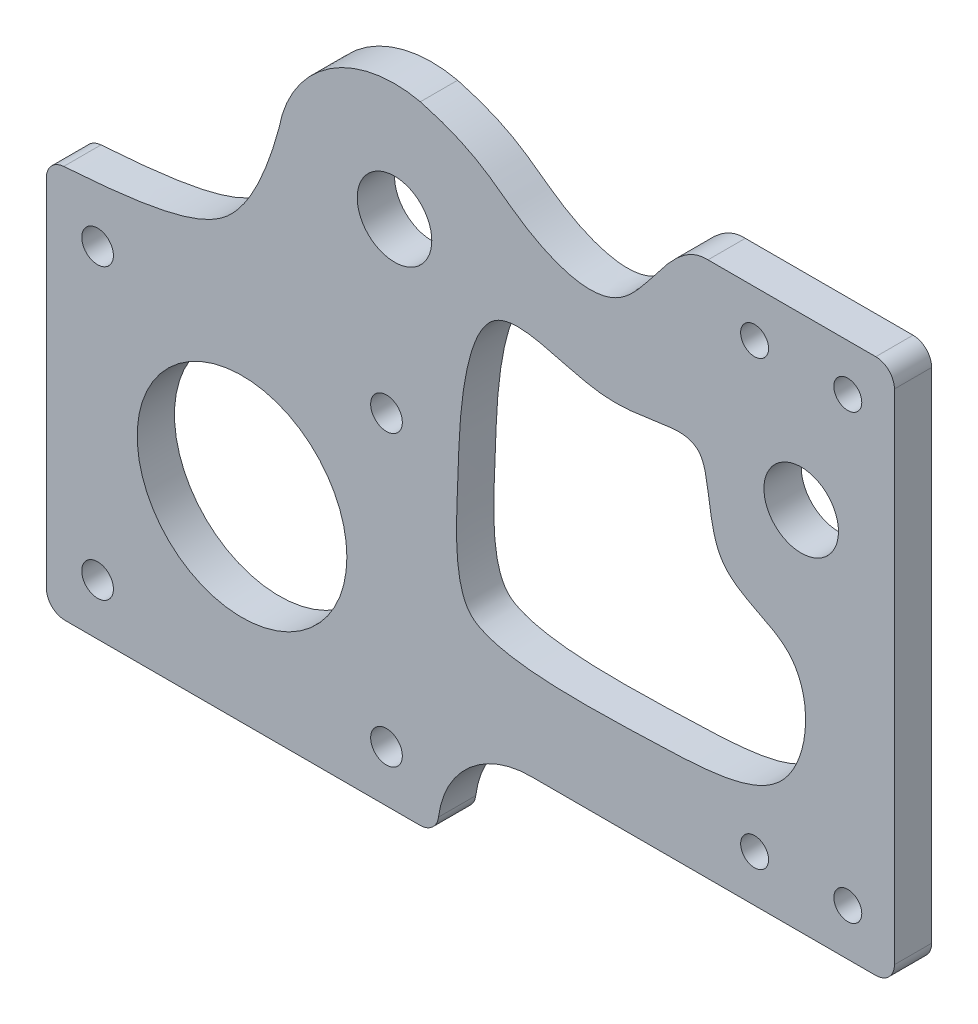
SolidWorks part; units mm, degrees
ref_plane "Front" through (0, 0, 0) normal (0, 0, 1) x (1, 0, 0)
ref_plane "Top" through (0, 0, 0) normal (0, 1, 0) x (1, 0, 0)
ref_plane "Right" through (0, 0, 0) normal (1, 0, 0) x (0, 0, -1)
sketch "Эскиз1" plane through (0, 0, 0) normal (0, 0, 1) x (1, 0, 0)
  line L0 (0, 31.4606) -> (0, -31.4606) construction
  line L1 (-31.2548, 0) -> (31.1288, 0) construction
  line L2 (33.4427, -49.75) -> (-102.9209, -49.75)
  line L3 (-39, -49.75) -> (-81, -49.75)
  line L4 (-39, -49.75) -> (-39, -7.75)
  line L5 (-39, -7.75) -> (-81, -7.75)
  line L6 (-81, -49.75) -> (-81, -7.75)
  line L7 (-39, -49.75) -> (-81, -7.75) construction
  line L8 (-39, -7.75) -> (-81, -49.75) construction
  line L9 (-39, -39.25) -> (10, -39.25)
  line L10 (10, -39.25) -> (10, 18.25)
  line L11 (10, 18.25) -> (-10, 18.25)
  circle A0 centre (0, 0) radius 31.35 construction
  circle A1 centre (-43.6395, 5.215) radius 12.6
  circle A2 centre (-60, -28.75) radius 12.6 construction
  circle A3 centre (-43.6395, 5.215) radius 25.1 construction
  circle A4 centre (-43.6395, 5.215) radius 4
  circle A5 centre (0, 0) radius 4
  circle A6 centre (-75.5, -13.25) radius 1.7
  circle A7 centre (-75.5, -44.25) radius 1.7
  circle A8 centre (-44.5, -44.25) radius 1.7
  circle A9 centre (-44.5, -13.25) radius 1.7
  circle A10 centre (-5, 13.25) radius 1.5
  circle A11 centre (5, 13.25) radius 1.5
  circle A12 centre (5, -34.25) radius 1.5
  circle A13 centre (-5, -34.25) radius 1.5
  circle A14 centre (-60, -28.75) radius 11.25
  spline S0 degree 3 poles (-81, -7.75) (-71.2884, -7.1899) (-65.2187, -6.0729) (-59.2532, -1.9596) (-57.1407, 3.3446) (-56.0334, 7.4846) knots 0 0 0 0 0.434692 0.534692 1 1 1 1
  spline S1 degree 3 poles (-40.8667, 17.5062) (-34.6739, 15.8351) (-31.1483, 11.5627) (-18.0784, 6.1668) (-13.9697, 18.3912) (-10, 18.25) knots 0 0 0 0 0.320222 0.646275 1 1 1 1
  dimension "D1" = 62.7
  dimension "D2" = 50.2
  dimension "D3" = 25.2
  dimension "D7" = 8
  dimension "D8" = 3.4
  dimension "D15" = 3
  dimension "D19" = 22.5
  dimension "D4" = 42
  dimension "D5" = 49.75
  dimension "D6" = 60
  dimension "D9" = 31
  dimension "D10" = 31
  dimension "D11" = 10
  dimension "D12" = 10
  dimension "D13" = 47.5
  dimension "D14" = 13.25
  dimension "D16" = 5
  dimension "D17" = 5
  dimension "D18" = 5
  dimension "D20" = 20
extrude "Бобышка-Вытянуть1" add sketch "Эскиз1" along normal blind 4
fillet "Скругление1" radius 10 1 edges at (-39, -39.25, 2)
fillet "Скругление2" radius 2 5 edges at (10, 18.25, 2) (10, -39.25, 2) (-81, -7.75, 2) (-39, -49.75, 2) (-81, -49.75, 2)
sketch "Эскиз3" plane through (0, 0, 4) normal (0, 0, 1) x (1, 0, 0)
  spline S0 degree 3 poles (-37.5345, -26.2489) (-31.6938, -29.9849) (-15.5061, -29.5218) (0.4262, -28.9341) (1.724, -12.3756) (-10.3351, -11.1175) (-9.6922, -1.1593) (-12.5627, 1.3847) (-16.2082, 0.049) (-24.5772, -0.1066) (-34.8944, 5.7107) (-36.6751, -8.7803) (-36.8542, -17.7168) (-37.5345, -26.2489) (-31.6938, -29.9849) (-15.5061, -29.5218) knots -0.127236 -0.103063 -0.011451 0 0.116396 0.228688 0.343685 0.433681 0.51387 0.533563 0.61982 0.643369 0.758274 0.872764 0.896937 0.988549 1 1.116396 1.228688 1.343685 only from (-34.445, -28.1789) to (-34.445, -28.1789)
extrude "Вырез-Вытянуть1" cut sketch "Эскиз3" against normal through all
